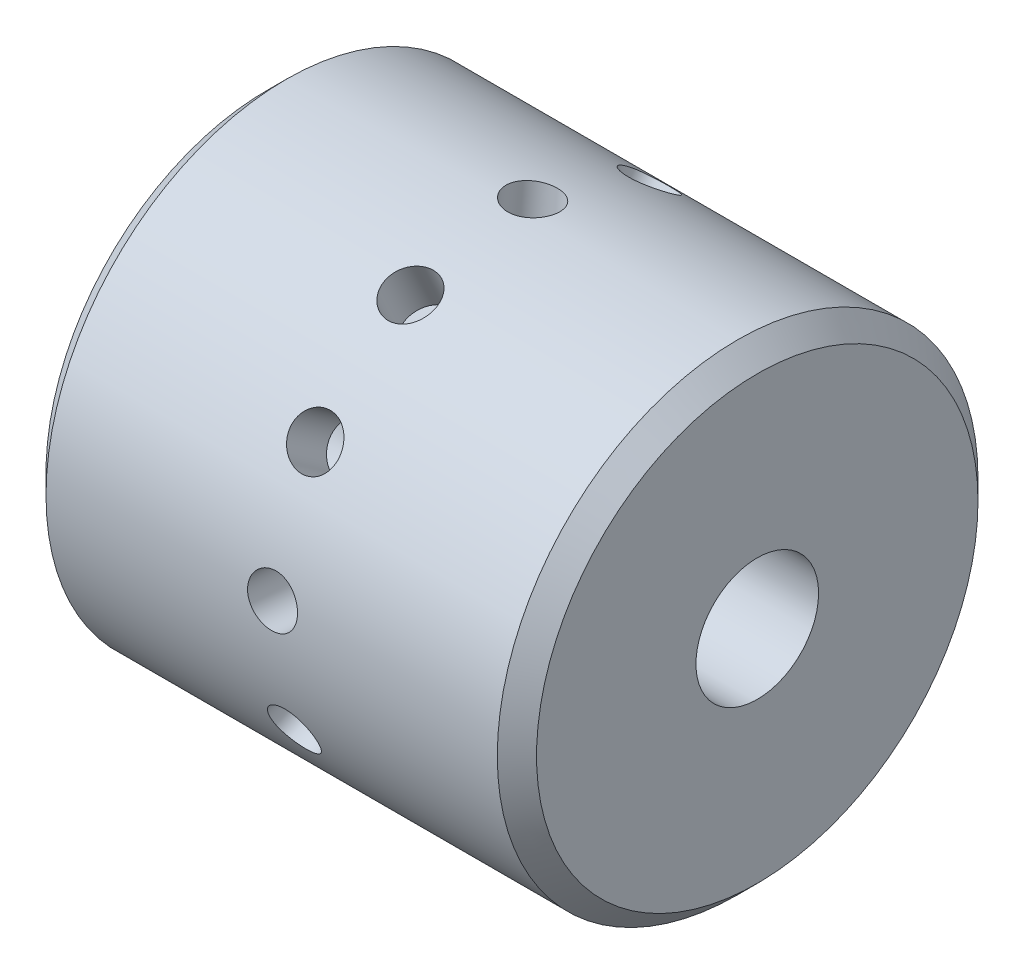
SolidWorks part; units mm, degrees
material "Brass"
ref_plane "Front Plane" through (0, 0, 0) normal (0, 0, 1) x (1, 0, 0)
ref_plane "Top Plane" through (0, 0, 0) normal (0, 1, 0) x (1, 0, 0)
ref_plane "Right Plane" through (0, 0, 0) normal (1, 0, 0) x (0, 0, -1)
sketch "Sketch1" plane through (0, 0, 0) normal (1, 0, 0) x (0, 0, -1)
  circle A0 centre (0, 0) radius 12.446
  dimension "D1" = 24.892
extrude "Boss-Extrude1" add sketch "Sketch1" along normal mid plane 25.4
chamfer "Chamfer1" distance 1.016 angle 45 1 edges at (12.7, 0, -12.446)
chamfer "Chamfer2" distance 1.016 angle 45 1 edges at (-12.7, 0, -12.446)
sketch "Sketch2" plane through (12.7, 0, 0) normal (1, 0, 0) x (0, 0, -1)
  circle A0 centre (0, 0) radius 3.175
  circle A1 centre (0, 0) radius 11.43 construction
  dimension "D1" = 6.35
extrude "Cut-Extrude1" cut sketch "Sketch2" against normal up to surface (25.4 mm away) up to face at (-12.7, 0, -11.43)
sketch "Sketch3" plane through (0, 0, 0) normal (1, 0, 0) x (0, 0, -1)
  circle A0 centre (0, 0) radius 12.446
  circle A1 centre (0, 0) radius 12.446 construction
hole_wizard "#38 (0.1015) Diameter Hole1" positions "3DSketch5" profile "Sketch4" hole size "#38" standard "ANSI Inch"
sketch3d "3DSketch5"
  circle A0 centre (0, 0, 0) radius 12.446 construction
  point P0 (0, 10.2172, -7.1072)
  point P4 (12.446, 0, 0)
  point P5 (0, 10.2025, -7.1283)
sketch "Sketch4" plane through (0, 10.2025, -7.1283) normal (1, 0, 0) x (0, 0.5727, 0.8197)
  line L0 (0, 0) -> (0, 3.3145)
  line L1 (0, 3.3145) -> (1.289, 2.54)
  line L2 (1.289, 2.54) -> (1.289, 0)
  line L5 (1.289, 0) -> (0, 0)
  line L10 (0, 3.3145) -> (-1.289, 2.54) construction
  line L11 (0, -6.35) -> (0, 107.95) construction
  dimension "Hole Dia." = 2.5781
  dimension "Hole Depth" = 2.54
  dimension "Drill Angle" = 118
pattern_circular "CirPattern4" count 12 over 360 about axis through (12.7, 0, 0) along (-1, 0, 0) of "#38 (0.1015) Diameter Hole1"
